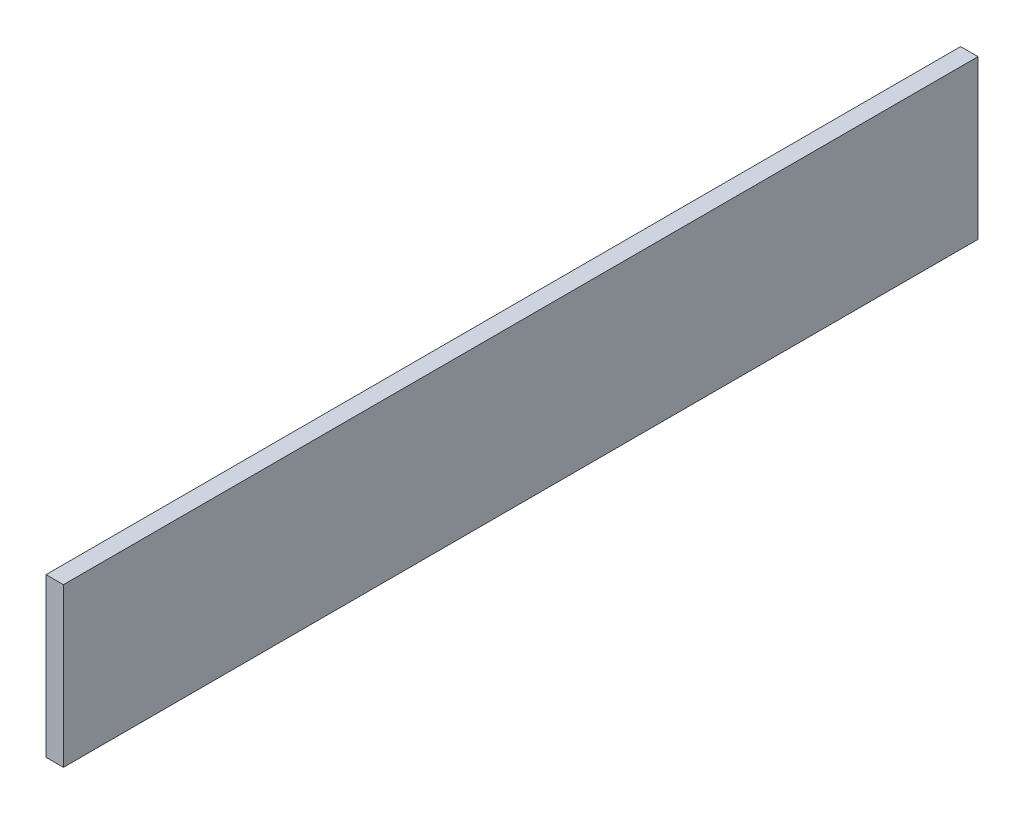
SolidWorks part; units mm, degrees
ref_plane "Ebene vorne" through (0, 0, 0) normal (0, 0, 1) x (1, 0, 0)
ref_plane "Ebene oben" through (0, 0, 0) normal (0, 1, 0) x (1, 0, 0)
ref_plane "Ebene rechts" through (0, 0, 0) normal (1, 0, 0) x (0, 0, -1)
sketch "Sketch1" plane through (0, 0, 0) normal (1, 0, 0) x (0, 0, -1)
  line L1 (-578, -100) -> (578, -100)
  line L2 (-578, -100) -> (-578, 100)
  line L3 (-578, 100) -> (578, 100)
  line L4 (578, -100) -> (578, 100)
  line L5 (-578, -100) -> (578, 100) construction
  line L6 (-578, 100) -> (578, -100) construction
  point P0 (0, 0)
  dimension "D1" = 1156
  dimension "D2" = 200
extrude "Boss-Extrude1" add sketch "Sketch1" along normal blind 22
